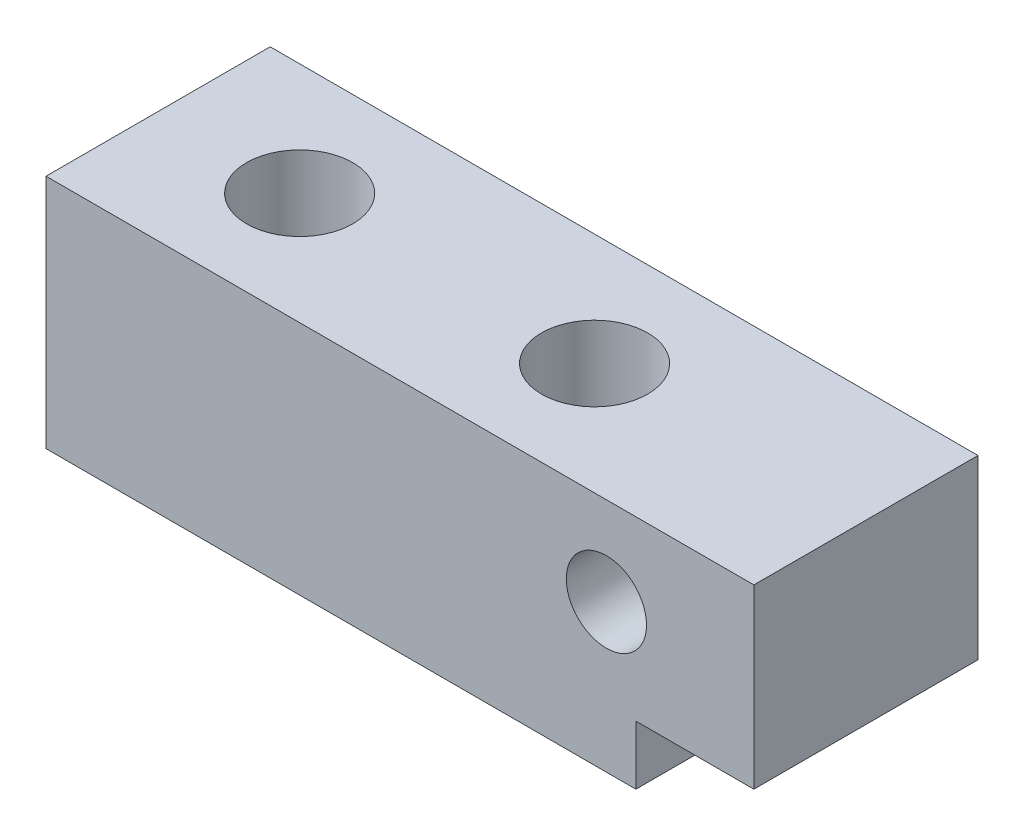
SolidWorks part; units mm, degrees
ref_plane "Front" through (0, 0, 0) normal (0, 0, 1) x (1, 0, 0)
ref_plane "Top" through (0, 0, 0) normal (0, 1, 0) x (1, 0, 0)
ref_plane "Right" through (0, 0, 0) normal (1, 0, 0) x (0, 0, -1)
sketch "Sketch1" plane through (0, 0, 0) normal (0, 0, 1) x (1, 0, 0)
  line L1 (0, 0) -> (60, 0)
  line L2 (0, 0) -> (0, 20)
  line L3 (0, 20) -> (60, 20)
  line L4 (60, 0) -> (60, 20)
  dimension "D1" = 20
  dimension "D2" = 60
extrude "Boss-Extrude1" add sketch "Sketch1" against normal mid plane 19
sketch "Sketch2" plane through (0, 0, 9.5) normal (0, 0, 1) x (1, 0, 0)
  line L0 (0, 20) -> (0, 0) construction
  line L1 (60, 0) -> (50, 0)
  line L2 (60, 0) -> (60, 5)
  line L3 (60, 5) -> (50, 5)
  line L4 (50, 0) -> (50, 5)
  dimension "D1" = 50
  dimension "D2" = 5
extrude "Cut-Extrude1" cut sketch "Sketch2" against normal through all
hole_wizard "Ø9.0 (9) Diameter Hole1" positions "Sketch4" profile "Sketch3" hole size "Ø9.0" standard "JIS" end condition through all
sketch "Sketch4" plane through (0, 20, 0) normal (0, 1, 0) x (-1, 0, 0)
  line L0 (0, -9.5) -> (0, 9.5) construction
  point P0 (-12, 0)
  point P1 (-37, 0)
  dimension "D1" = 12
  dimension "D2" = 25
sketch "Sketch3" plane through (12, 20, 0) normal (1, 0, 0) x (0, 0, 1)
  line L0 (0, 0) -> (0, 20)
  line L1 (0, 20) -> (4.5, 20)
  line L2 (4.5, 20) -> (4.5, 0)
  line L5 (4.5, 0) -> (0, 0)
  line L11 (0, -6.35) -> (0, 107.95) construction
  dimension "Thru Hole Dia." = 9
  dimension "Thru Hole Depth" = 20
hole_wizard "M8x1.25 Tapped Hole1" positions "Sketch6" profile "Sketch5" tap size "M8x1.25" standard "JIS" end condition through all
sketch "Sketch6" plane through (0, 0, 9.5) normal (0, 0, 1) x (1, 0, 0)
  line L0 (0, 0) -> (50, 0) construction
  line L1 (0, 20) -> (0, 0) construction
  point P0 (47.5, 12.5)
  dimension "D1" = 12.5
  dimension "D2" = 47.5
sketch "Sketch5" plane through (47.5, 12.5, 9.5) normal (1, 0, 0) x (0, -1, 0)
  line L0 (0, 0) -> (0, 19)
  line L1 (0, 19) -> (3.4, 19)
  line L2 (3.4, 19) -> (3.4, 0)
  line L5 (3.4, 0) -> (0, 0)
  line L11 (0, -6.35) -> (0, 107.95) construction
  dimension "Thru Tap Drill Dia." = 6.8
  dimension "Thru Tap Drill Depth" = 19
cosmetic thread "Hole Thread1" parameters "D2"=8
